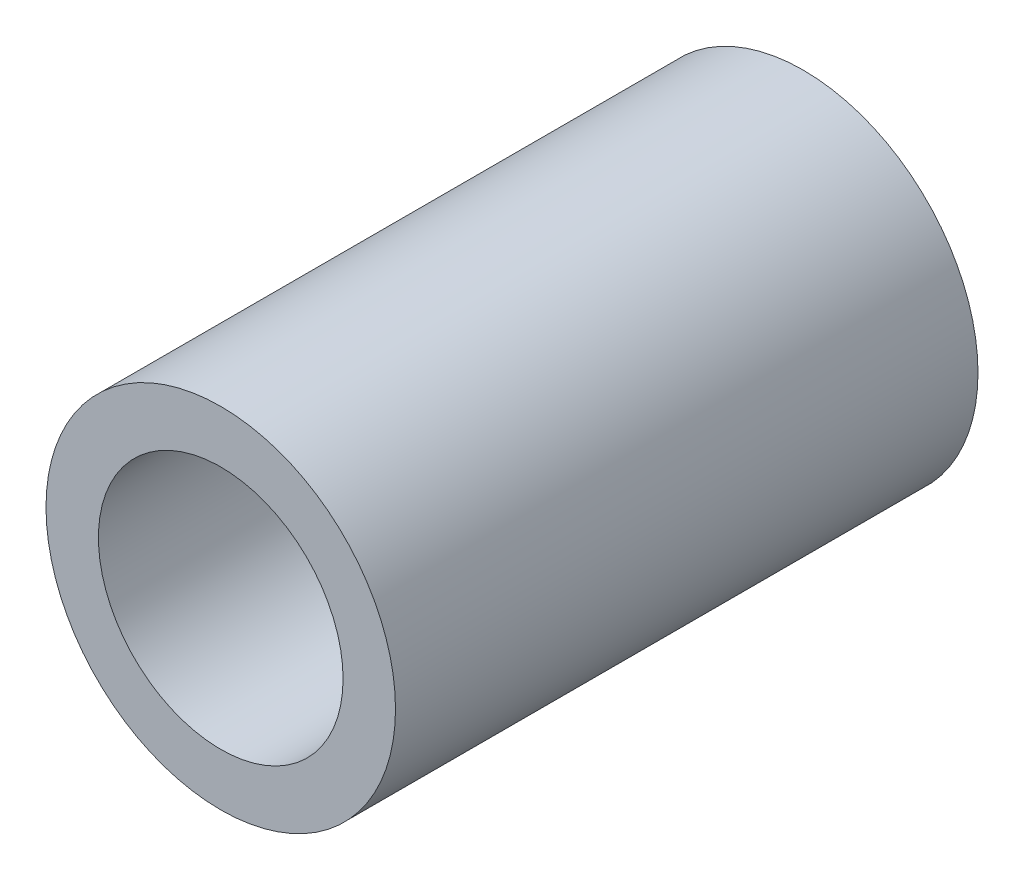
SolidWorks part; units mm, degrees
ref_plane "Front Plane" through (0, 0, 0) normal (0, 0, 1) x (1, 0, 0)
ref_plane "Top Plane" through (0, 0, 0) normal (0, 1, 0) x (1, 0, 0)
ref_plane "Right Plane" through (0, 0, 0) normal (1, 0, 0) x (0, 0, -1)
sketch "Sketch1" plane through (0, 0, 0) normal (0, 0, 1) x (1, 0, 0)
  circle A0 centre (0, 0) radius 3
  circle A1 centre (0, 0) radius 2.1
  dimension "OD" = 6
  dimension "ID" = 4.2
extrude "Extrude1" add sketch "Sketch1" along normal mid plane 10
sketch "Sketch2" plane through (0, 0, 0) normal (1, 0, 0) x (0, 0, -1)
  line L0 (-5, -2.1) -> (5, -2.1) construction
  line L3 (5, 2.1) -> (-5, 2.1) construction
  line L5 (-5, -2.1) -> (5, -2.1)
  line L6 (5, 2.1) -> (-5, 2.1)
sketch "Sketch4" plane through (0, 0, 5) normal (0, 0, 1) x (1, 0, 0)
  line L0 (0, 0) -> (-1.4849, 1.4849)
  line L1 (0, -1.1) -> (0, 1.1) construction
  circle A0 centre (0, 0) radius 2.1 construction
  dimension "D1" = 45
